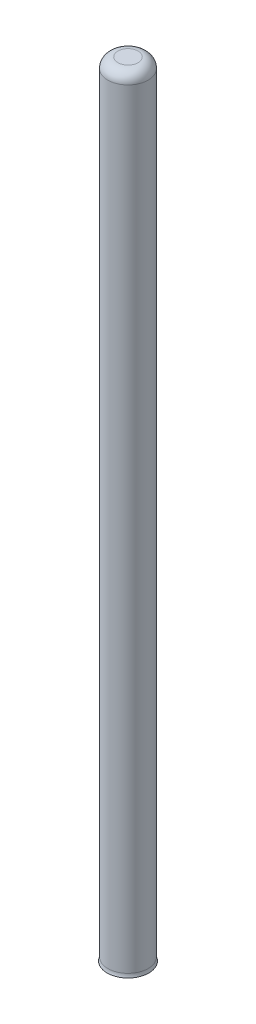
SolidWorks part; units mm, degrees
ref_plane "Front Plane" through (0, 0, 0) normal (0, 0, 1) x (1, 0, 0)
ref_plane "Top Plane" through (0, 0, 0) normal (0, 1, 0) x (1, 0, 0)
ref_plane "Right Plane" through (0, 0, 0) normal (1, 0, 0) x (0, 0, -1)
sketch "Croquis1" plane through (0, 0, 0) normal (0, 1, 0) x (1, 0, 0)
  circle A0 centre (0, 0) radius 4
  dimension "D1" = 8
extrude "Saliente-Extruir1" add sketch "Croquis1" along normal blind 165
sketch "Croquis2" plane through (0, 0, 0) normal (0, -1, 0) x (1, 0, 0)
  line L0 (2.4058, 0.6799) -> (-1.3263, 2.1192) construction
  line L1 (-2.4058, -0.6799) -> (1.3263, -2.1192) construction
  line L2 (2.4058, 0.6799) -> (-1.3263, 2.1192)
  line L3 (-2.4058, -0.6799) -> (1.3263, -2.1192)
  line L4 (-2.4777, -0.8665) -> (1.2544, -2.3058)
  line L5 (2.4777, 0.8665) -> (-1.2544, 2.3058)
  line L6 (1.2544, -2.3058) -> (1.3455, -2.3409)
  line L7 (-2.4777, -0.8665) -> (-2.5688, -0.8314)
  line L8 (2.4777, 0.8665) -> (2.5688, 0.8314)
  line L9 (-1.2544, 2.3058) -> (-1.3455, 2.3409)
  circle A0 centre (0, 0) radius 2.5
  circle A1 centre (0, 0) radius 4
  circle A2 centre (0, 0) radius 4
  circle A3 centre (0, 0) radius 2.7
  dimension "D1" = 0
  dimension "D2" = 0.2
extrude "Cortar-Extruir1" cut sketch "Croquis2" against normal blind 7 contours L4 A0 L3 | L6 A3 L8 L5 A0 L4 | L2 A0 L5 | L9 A3 L7 L4 A0 L5 | L3 A0 L2
sketch "Croquis6" plane through (0, 0, 0) normal (0, -1, 0) x (1, 0, 0)
  circle A0 centre (0, 0) radius 7.5
  circle A2 centre (0, 0) radius 4
  circle A3 centre (0, 0) radius 4
  dimension "D1" = 15
  dimension "D2" = 0
extrude "Saliente-Extruir2" add sketch "Croquis6" against normal offset from surface (8 mm away) 1 up to face at (0, 7, 0) offset beyond the face yes
sketch "Croquis8" plane through (0, 0, 0) normal (0, 0, 1) x (1, 0, 0)
  line L0 (-7.5, 8) -> (-4, 8)
  line L1 (-4, 8) -> (-4, 9)
  line L2 (-4, 165) -> (-4, 8) construction
  line L3 (-4, 9) -> (-7.5, 8)
  line L8 (0, 0) -> (0, 12.1729) construction
  dimension "D1" = 1
revolve "Revolución1" add sketch "Croquis8" angle 360 about L8
fillet "Redondeo1" radius 2 2 edges at (0, 0, -7.5) (0, 8, -7.5)
fillet "Redondeo2" radius 2 2 edges at (0, 9, -4) (0, 165, 4)
sketch "Croquis9" plane through (0, 0, 0) normal (0, -1, 0) x (1, 0, 0)
  circle A0 centre (0, 0) radius 9.5032
extrude "Cortar-Extruir2" cut sketch "Croquis9" against normal blind 9.8
